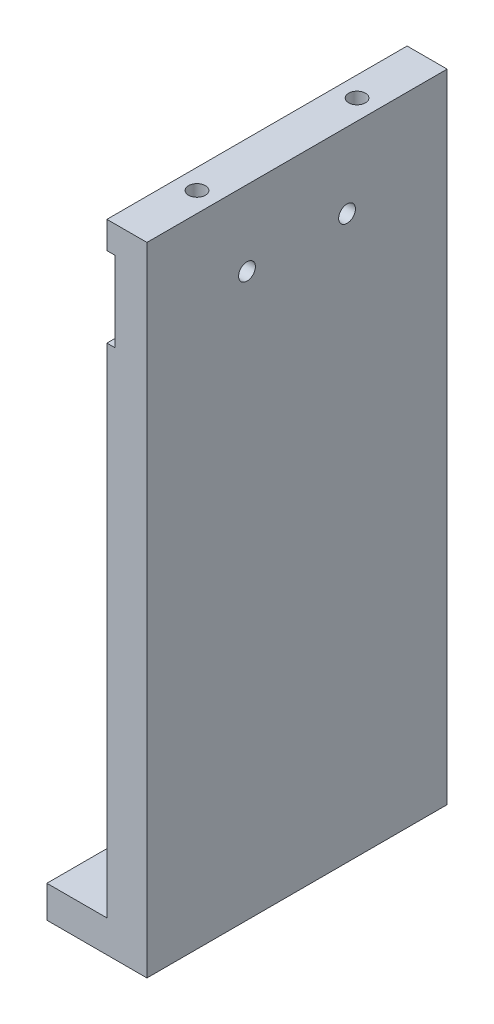
SolidWorks part; units mm, degrees
ref_plane "前视基准面" through (0, 0, 0) normal (0, 0, 1) x (1, 0, 0)
ref_plane "上视基准面" through (0, 0, 0) normal (0, 1, 0) x (1, 0, 0)
ref_plane "右视基准面" through (0, 0, 0) normal (1, 0, 0) x (0, 0, -1)
sketch "草图1" plane through (0, 0, 0) normal (0, 0, 1) x (1, 0, 0)
  line L1 (0, 0) -> (10, 0)
  line L2 (0, 0) -> (0, 159.15)
  line L3 (0, 159.15) -> (10, 159.15)
  line L4 (10, 0) -> (10, 159.15)
  dimension "D1" = 159.15
  dimension "D2" = 10
extrude "凸台-拉伸1" add sketch "草图1" along normal blind 75
hole_wizard "M5 螺纹孔1" positions "草图2" profile "草图3" tap size "M5" standard "ISO"
sketch "草图2" plane through (0, 159.15, 0) normal (0, 1, 0) x (1, 0, 0)
  point P0 (5, -57.5)
  point P3 (5, -17.5)
sketch "草图3" plane through (5, 159.15, 57.5) normal (1, 0, 0) x (0, 0, 1)
  line L0 (0, 0) -> (0, 13.6618)
  line L1 (0, 13.6618) -> (2.1, 12.4)
  line L2 (2.1, 12.4) -> (2.1, 0)
  line L5 (2.1, 0) -> (0, 0)
  line L10 (0, 13.6618) -> (-2.1, 12.4) construction
  line L11 (0, -6.35) -> (0, 107.95) construction
  dimension "螺纹孔钻头直径" = 4.2
  dimension "螺纹孔钻头深度" = 12.4
  dimension "导头角度" = 118
cosmetic thread "孔螺蚊线1" parameters "D1"=10, "D2"=5
cosmetic thread "孔螺蚊线2" parameters "D1"=10, "D2"=5
sketch "草图4" plane through (0, 0, 0) normal (-1, 0, 0) x (0, 0, 1)
  line L0 (0, 159.15) -> (0, 0) construction
  line L1 (0, 152.38) -> (75, 152.38)
  line L2 (0, 152.38) -> (0, 132.38)
  line L3 (0, 132.38) -> (75, 132.38)
  line L4 (75, 152.38) -> (75, 132.38)
  line L5 (75, 159.15) -> (75, 0) construction
  line L6 (75, 0) -> (0, 0) construction
  dimension "D1" = 20
  dimension "D2" = 132.38
extrude "切除-拉伸1" cut sketch "草图4" against normal blind 2
hole_wizard "M5 螺纹孔2" positions "草图5" profile "草图6" tap size "M5" standard "ISO"
sketch "草图5" plane through (2, 0, 0) normal (-1, 0, 0) x (0, 0, 1)
  line L0 (37.5, 152.38) -> (37.5, 126.9528) construction
  line L1 (75, 152.38) -> (0, 152.38) construction
  line L3 (0, 132.38) -> (75, 132.38) construction
  point P3 (25, 140.3817)
  point P5 (50, 140.3817)
  dimension "D1" = 25
  dimension "D2" = 8.0017
sketch "草图6" plane through (2, 140.3817, 25) normal (0, 1, 0) x (0, 0, 1)
  line L0 (0, 0) -> (0, 13.6618)
  line L1 (0, 13.6618) -> (2.1, 12.4)
  line L2 (2.1, 12.4) -> (2.1, 0)
  line L5 (2.1, 0) -> (0, 0)
  line L10 (0, 13.6618) -> (-2.1, 12.4) construction
  line L11 (0, -6.35) -> (0, 107.95) construction
  dimension "螺纹孔钻头直径" = 4.2
  dimension "螺纹孔钻头深度" = 12.4
  dimension "导头角度" = 118
cosmetic thread "孔螺蚊线3" parameters "D1"=8, "D2"=5
cosmetic thread "孔螺蚊线4" parameters "D1"=8, "D2"=5
sketch "草图7" plane through (0, 0, 0) normal (-1, 0, 0) x (0, 0, 1)
  line L0 (75, 132.38) -> (75, 0) construction
  line L1 (0, 0) -> (75, 0)
  line L2 (0, 0) -> (0, 8)
  line L3 (0, 8) -> (75, 8)
  line L4 (75, 0) -> (75, 8)
  dimension "D1" = 8
extrude "凸台-拉伸2" add sketch "草图7" along normal blind 15
sketch "草图8" plane through (0, 8, 0) normal (0, 1, 0) x (1, 0, 0)
  line L0 (-7.5, 0) -> (-7.5, -75) construction
  line L1 (-15, 0) -> (0, 0) construction
  line L2 (-15, -75) -> (0, -75) construction
  line L3 (-7.5, -75) -> (-7.5, -37.5) construction
  line L4 (-7.5, -37.5) -> (14.6827, -37.5) construction
  circle A0 centre (-7.5, -17.5) radius 3.25
  circle A1 centre (-7.5, -57.5) radius 3.25
  dimension "D1" = 6.5
  dimension "D2" = 40
extrude "切除-拉伸2" cut sketch "草图8" against normal through all
